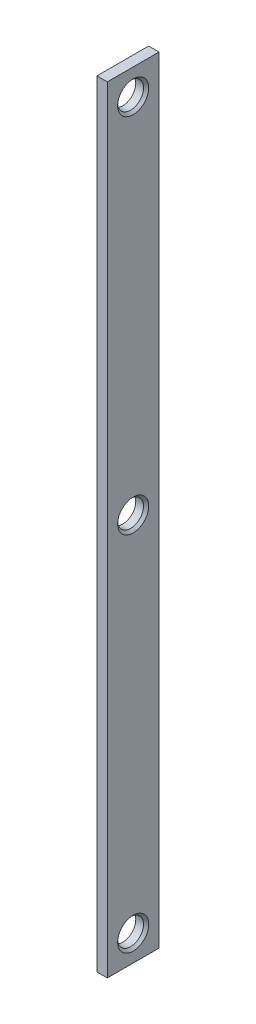
SolidWorks part; units mm, degrees
ref_plane "Спереди" through (0, 0, 0) normal (0, 0, 1) x (1, 0, 0)
ref_plane "Сверху" through (0, 0, 0) normal (0, 1, 0) x (1, 0, 0)
ref_plane "Справа" through (0, 0, 0) normal (1, 0, 0) x (0, 0, -1)
sketch "Эскиз1" plane through (0, 0, 0) normal (0, 1, 0) x (1, 0, 0)
  line L1 (-2, 10) -> (2, 10)
  line L2 (-2, 10) -> (-2, -10)
  line L3 (-2, -10) -> (2, -10)
  line L4 (2, 10) -> (2, -10)
  line L5 (-2, 10) -> (2, -10) construction
  line L6 (-2, -10) -> (2, 10) construction
  point P0 (0, 0)
extrude "Бобышка-Вытянуть1" add sketch "Эскиз1" along normal blind 300
sketch "Эскиз2" plane through (2, 0, 0) normal (1, 0, 0) x (0, 0, -1)
  circle A0 centre (0, 290) radius 5
  circle A1 centre (0, 150) radius 5
  circle A2 centre (0, 10) radius 5
  dimension "D1" = 3
extrude "Вырез-Вытянуть1" cut sketch "Эскиз2" against normal through all
chamfer "Фаска1" distance 1 angle 45 3 edges at (2, 10, -5) (2, 150, -5) (2, 290, -5)
